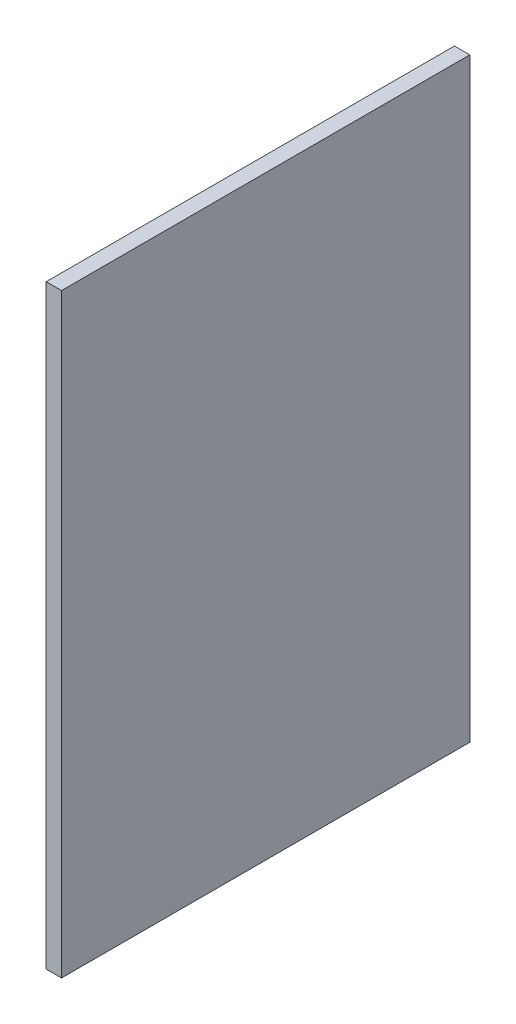
SolidWorks part; units mm, degrees
ref_plane "Front Plane" through (0, 0, 0) normal (0, 0, 1) x (1, 0, 0)
ref_plane "Top Plane" through (0, 0, 0) normal (0, 1, 0) x (1, 0, 0)
ref_plane "Right Plane" through (0, 0, 0) normal (1, 0, 0) x (0, 0, -1)
sketch "Sketch1" plane through (0, 0, 0) normal (1, 0, 0) x (0, 0, -1)
  line L1 (445.4965, -655.8904) -> (-34.5035, -655.8904)
  line L2 (445.4965, -655.8904) -> (445.4965, 44.1096)
  line L3 (445.4965, 44.1096) -> (-34.5035, 44.1096)
  line L4 (-34.5035, -655.8904) -> (-34.5035, 44.1096)
  dimension "D1" = 480
  dimension "D2" = 700
extrude "Boss-Extrude1" add sketch "Sketch1" along normal blind 18
